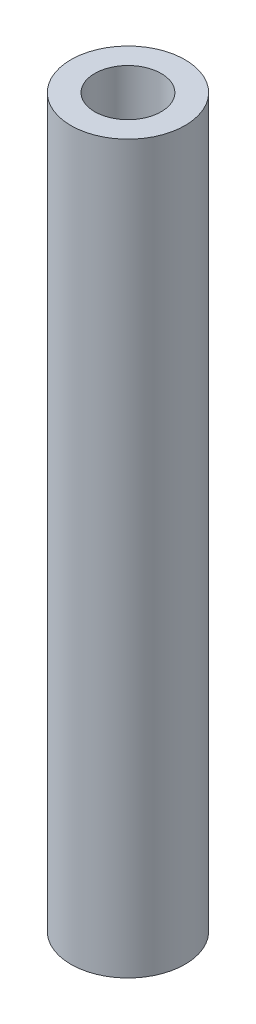
SolidWorks part; units mm, degrees
ref_plane "Front" through (0, 0, 0) normal (0, 0, 1) x (1, 0, 0)
ref_plane "Top" through (0, 0, 0) normal (0, 1, 0) x (1, 0, 0)
ref_plane "Right" through (0, 0, 0) normal (1, 0, 0) x (0, 0, -1)
sketch "Sketch1" plane through (0, 0, 0) normal (0, 1, 0) x (1, 0, 0)
  circle A0 centre (0, 0) radius 1.6
  circle A1 centre (0, 0) radius 2.75
  dimension "D1" = 3.2
  dimension "D2" = 5.5
extrude "Boss-Extrude1" add sketch "Sketch1" along normal blind 35
